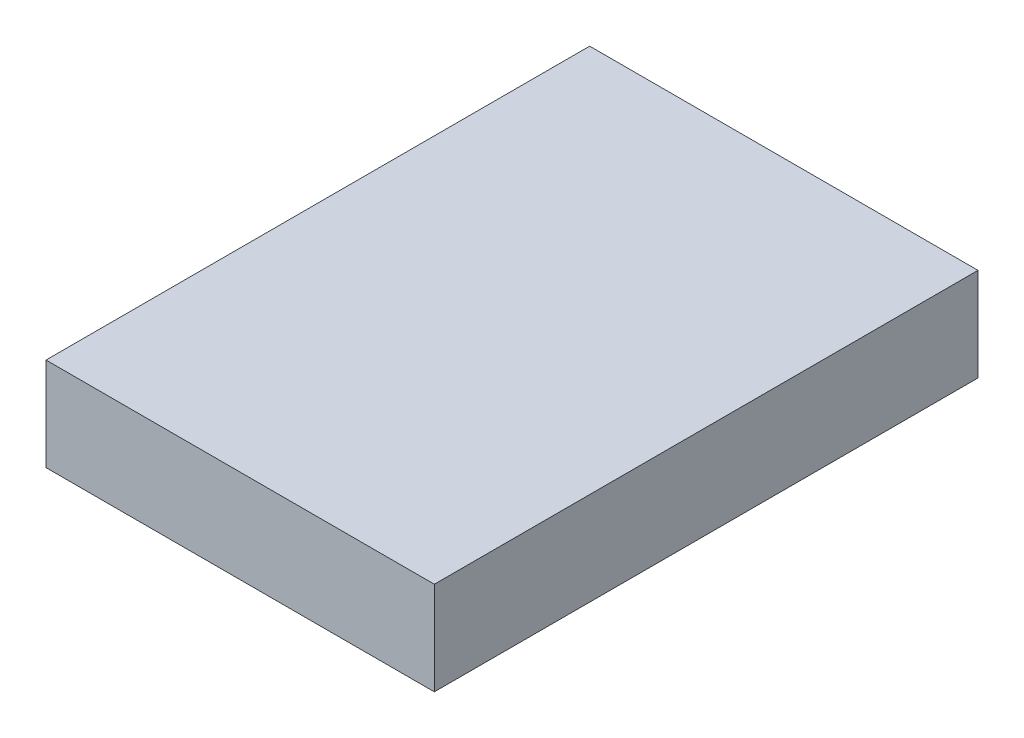
SolidWorks part; units mm, degrees
ref_plane "前视基准面" through (0, 0, 0) normal (0, 0, 1) x (1, 0, 0)
ref_plane "上视基准面" through (0, 0, 0) normal (0, 1, 0) x (1, 0, 0)
ref_plane "右视基准面" through (0, 0, 0) normal (1, 0, 0) x (0, 0, -1)
sketch "草图1" plane through (0, 0, 0) normal (0, 1, 0) x (1, 0, 0)
  line L1 (-6.25, 8.75) -> (6.25, 8.75)
  line L2 (-6.25, 8.75) -> (-6.25, -8.75)
  line L3 (-6.25, -8.75) -> (6.25, -8.75)
  line L4 (6.25, 8.75) -> (6.25, -8.75)
  line L5 (-6.25, 8.75) -> (6.25, -8.75) construction
  line L6 (-6.25, -8.75) -> (6.25, 8.75) construction
  point P0 (0, 0)
  dimension "D1" = 17.5
  dimension "D2" = 12.5
extrude "凸台-拉伸1" add sketch "草图1" along normal blind 3
